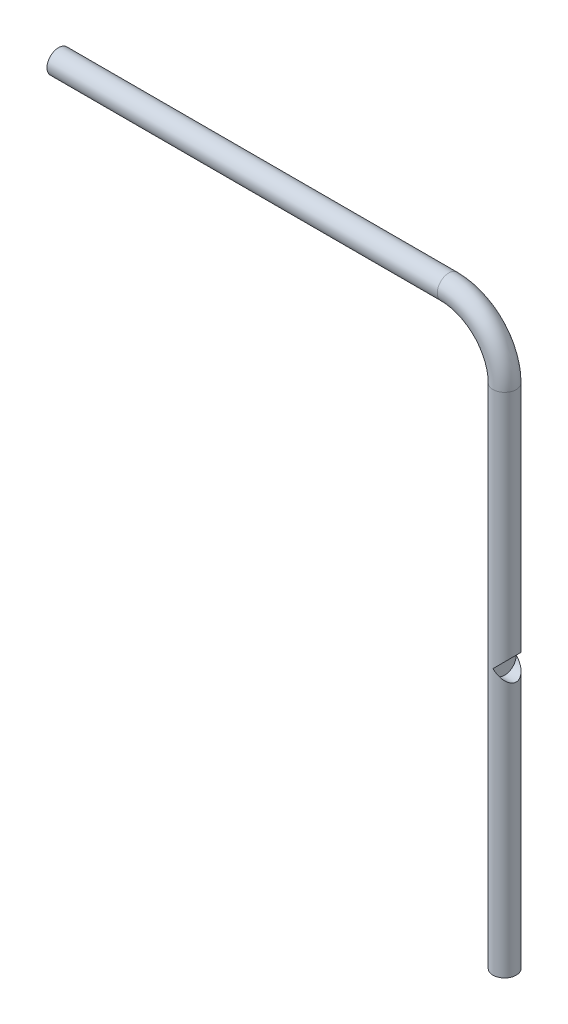
SolidWorks part; units mm, degrees
ref_plane "Front Plane" through (0, 0, 0) normal (0, 0, 1) x (1, 0, 0)
ref_plane "Top Plane" through (0, 0, 0) normal (0, 1, 0) x (1, 0, 0)
ref_plane "Right Plane" through (0, 0, 0) normal (1, 0, 0) x (0, 0, -1)
sketch "Sketch1" plane through (0, 0, 0) normal (0, 0, 1) x (1, 0, 0)
  line L0 (0, 0) -> (0, 495)
  line L1 (-60, 555) -> (-480, 555)
  arc A0 (0, 495) -> (-60, 555) centre (-60, 495) ccw
  dimension "D2" = 60
  dimension "D1" = 495
  dimension "D3" = 420
sweep "Sweep1" add path "Sketch1" circular profile diameter 25 parameters "D3"=25
sketch "Sketch2" plane through (0, 0, 0) normal (0, -1, 0) x (1, 0, 0)
  circle A0 centre (0, 0) radius 12.5
  circle A1 centre (0, 0) radius 12.5
  point P3 (0, 0)
  dimension "D1" = 25
sketch "Sketch5" plane through (0, 0, 0) normal (0, -1, 0) x (1, 0, 0)
  circle A0 centre (0, 0) radius 12.5
  dimension "D1" = 25
extrude "Boss-Extrude4" add sketch "Sketch2" along normal blind 50.79 contours A0
sketch "Sketch11" plane through (0, 0, 0) normal (1, 0, 0) x (0, 0, -1)
  line L0 (0, 495) -> (0, 235) construction
  line L1 (12.5, 495) -> (-12.5, 495) construction
  circle A0 centre (0, 235) radius 12.5
  dimension "D2" = 25
  dimension "D1" = 260
extrude "Cut-Extrude2" cut sketch "Sketch11" along normal blind 50.79
